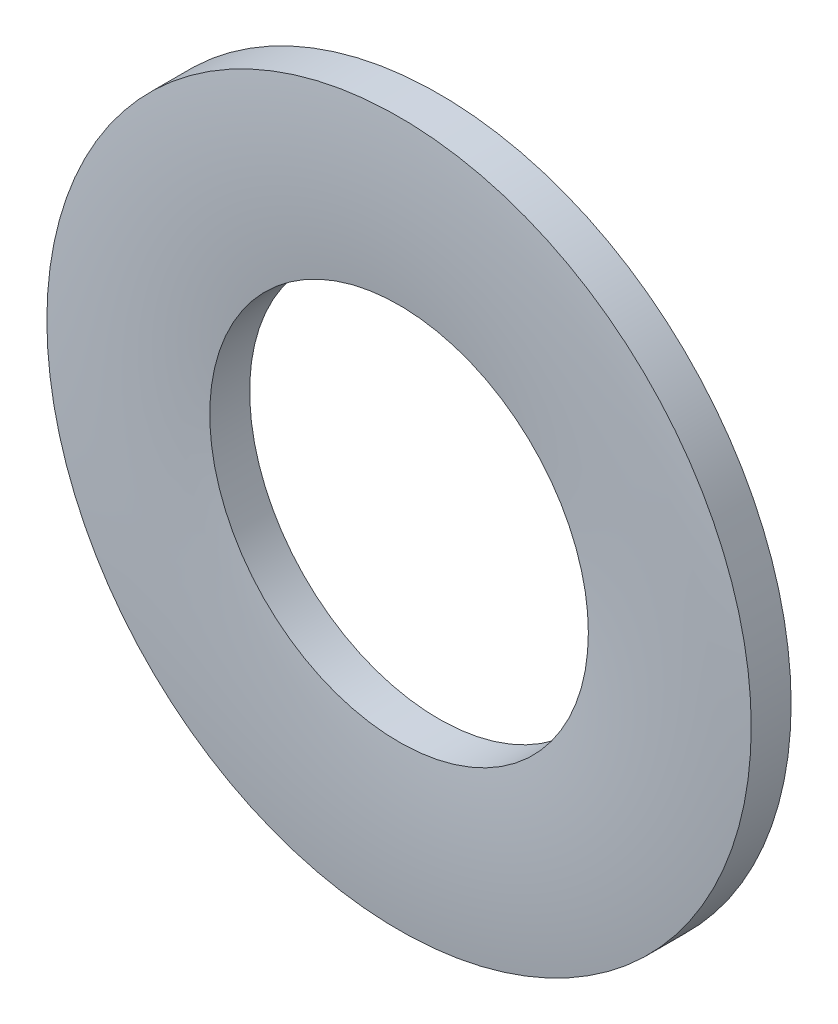
SolidWorks part; units mm, degrees
ref_plane "Front Plane" through (0, 0, 0) normal (0, 0, 1) x (1, 0, 0)
ref_plane "Top Plane" through (0, 0, 0) normal (0, 1, 0) x (1, 0, 0)
ref_plane "Right Plane" through (0, 0, 0) normal (1, 0, 0) x (0, 0, -1)
sketch "Sketch1" plane through (0, 0, 0) normal (0, 0, 1) x (1, 0, 0)
  circle A0 centre (0, 0) radius 2.15
  circle A1 centre (0, 0) radius 4
  dimension "ID" = 4.3
  dimension "OD" = 8
sketch "Sketch2" plane through (0, 0, 0) normal (1, 0, 0) x (0, 0, -1)
  line L0 (-0.25, 4) -> (0.25, 4) construction
  line L1 (-0.25, 0) -> (0.25, 0) construction
  point P2 (0, 4)
  dimension "Thickness Range" = 0.5
sketch "Sketch3" plane through (0, 0, 0) normal (1, 0, 0) x (0, 0, -1)
  line L0 (0.25, 4) -> (-0.2031, 4)
  line L1 (0.25, 2.15) -> (-0.2031, 2.15)
  line L2 (0.25, 2.15) -> (0.25, 4)
  line L3 (-0.25, 4) -> (-0.25, 2.15) construction
  arc A0 (-0.2031, 2.15) -> (-0.2031, 4) centre (8.905, 3.075) cw
  point P9 (0, 2.15)
  dimension "D1" = 0.0469
revolve "Revolve1" add sketch "Sketch3" angle 360 about L1
equation "\"D1@Sketch3\"=\"Thickness Range@Sketch2\"*.0937"
